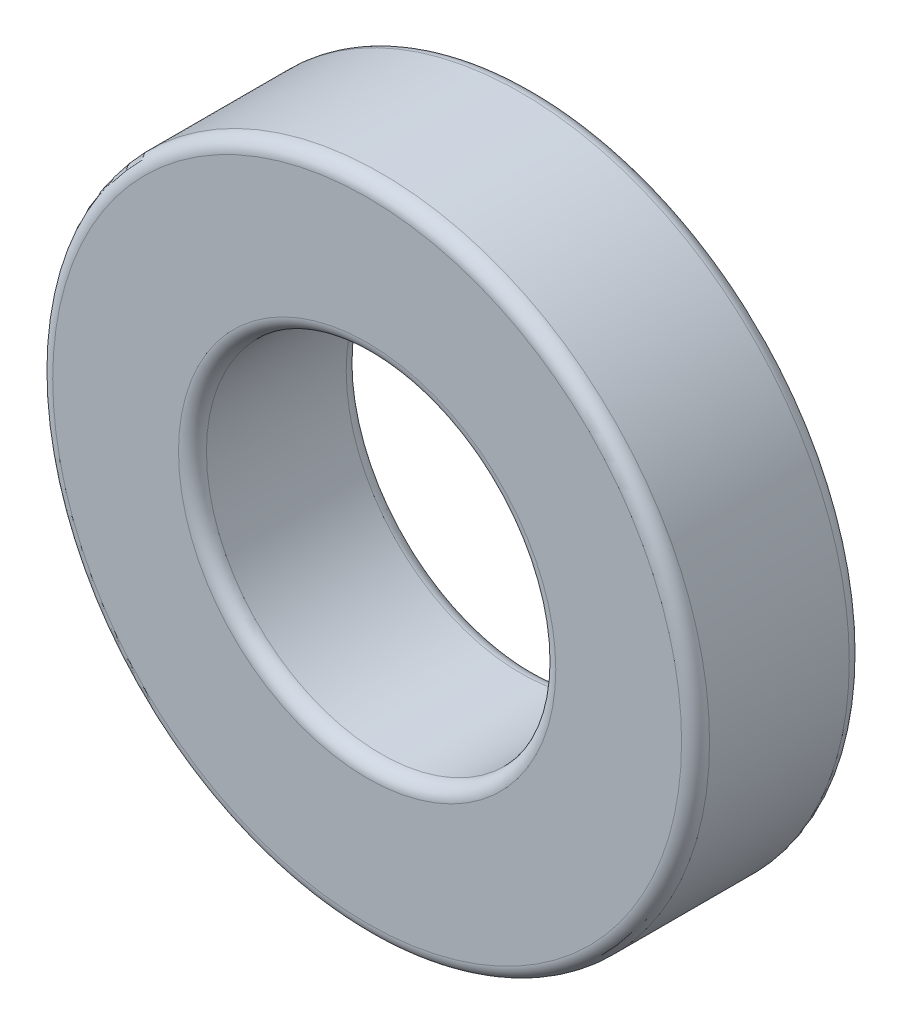
SolidWorks part; units mm, degrees
ref_plane "Front Plane" through (0, 0, 0) normal (0, 0, 1) x (1, 0, 0)
ref_plane "Top Plane" through (0, 0, 0) normal (0, 1, 0) x (1, 0, 0)
ref_plane "Right Plane" through (0, 0, 0) normal (1, 0, 0) x (0, 0, -1)
sketch "Sketch1" plane through (0, 0, 0) normal (0, 0, 1) x (1, 0, 0)
  circle A0 centre (0, 0) radius 23.5
  circle A1 centre (0, 0) radius 12.5
  dimension "D1" = 47
  dimension "D2" = 25
extrude "Boss-Extrude1" add sketch "Sketch1" along normal blind 12
fillet "Fillet1" radius 1 4 edges at (12.5, 0, 0) (12.5, 0, 12) (23.5, 0, 0) (23.5, 0, 12)
